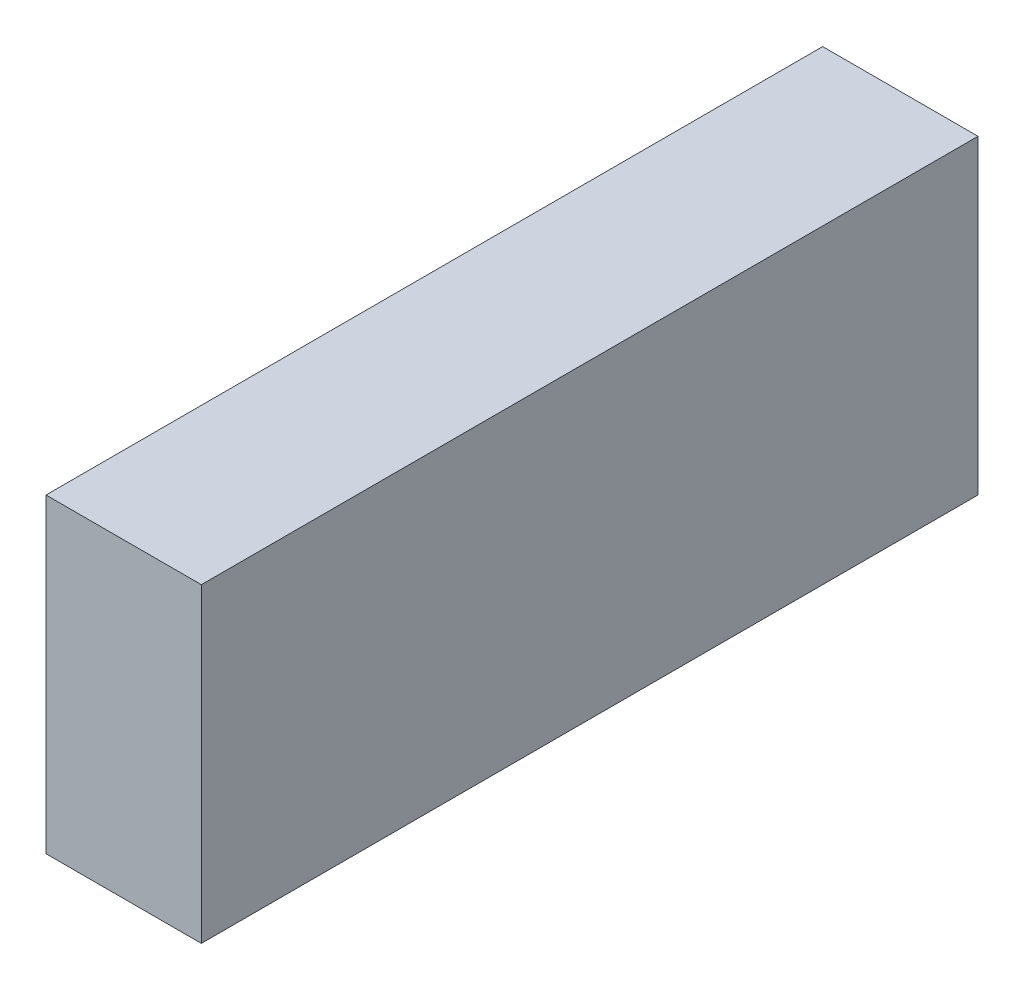
SolidWorks part; units mm, degrees
material "Unlegierter Baustahl"
ref_plane "Ebene vorne" through (0, 0, 0) normal (0, 0, 1) x (1, 0, 0)
ref_plane "Ebene oben" through (0, 0, 0) normal (0, 1, 0) x (1, 0, 0)
ref_plane "Ebene rechts" through (0, 0, 0) normal (1, 0, 0) x (0, 0, -1)
sketch "Skizze1" plane through (0, 0, 0) normal (0, 0, 1) x (1, 0, 0)
  line L1 (0, 0) -> (10, 0)
  line L2 (0, 0) -> (0, 20)
  line L3 (0, 20) -> (10, 20)
  line L4 (10, 0) -> (10, 20)
  dimension "D1" = 20
  dimension "D2" = 10
extrude "Linear austragen1" add sketch "Skizze1" along normal blind 50
